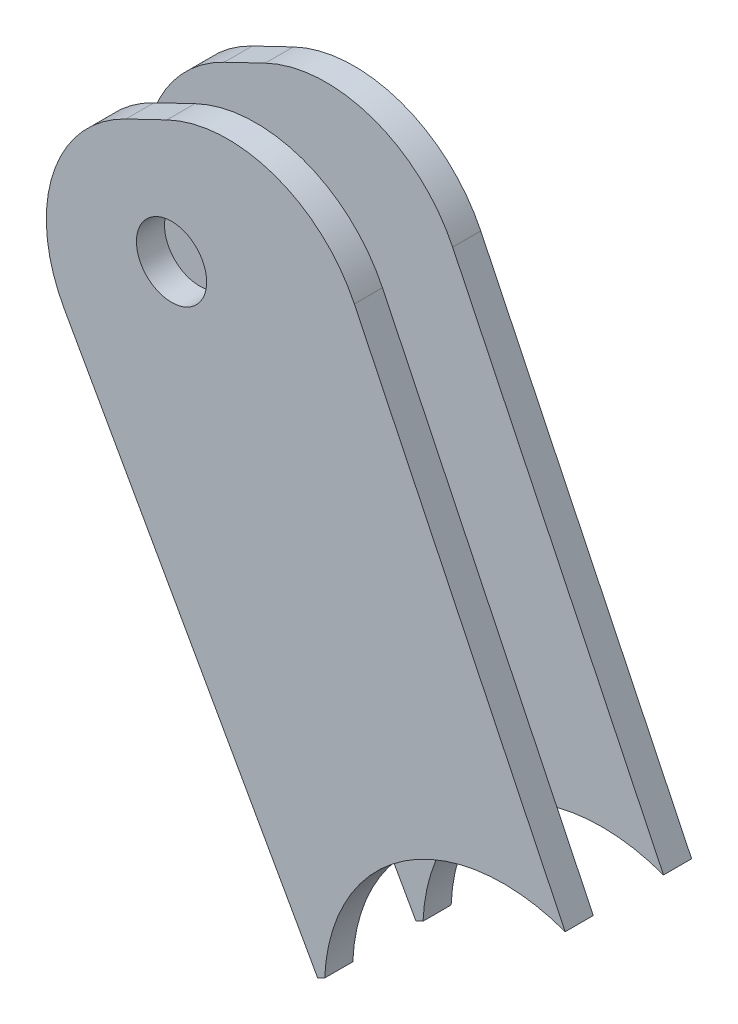
SolidWorks part; units mm, degrees
material "1.0037 (S235JR)"
ref_plane "Płaszczyzna XY" through (0, 0, 0) normal (0, 0, 1) x (1, 0, 0)
ref_plane "Płaszczyzna XZ" through (0, 0, 0) normal (0, 1, 0) x (1, 0, 0)
ref_plane "Płaszczyzna YZ" through (0, 0, 0) normal (1, 0, 0) x (0, 0, -1)
sketch "Szkic1" plane through (0, 0, 0) normal (0, 0, 1) x (1, 0, 0)
  line L0 (207.5316, 219.2375) -> (210.4517, 220.6423)
  line L5 (223.7984, 215.9663) -> (240.051, 182.1835)
  line L6 (240.051, 182.1835) -> (221.1833, 173.1064)
  line L7 (221.1833, 173.1064) -> (203.1408, 205.342)
  circle A2 centre (210.7813, 212.0576) radius 2.5 construction
  circle A3 centre (210.7813, 212.0576) radius 2.5
  arc A4 (210.4517, 220.6423) -> (223.7984, 215.9663) centre (214.787, 211.631) cw
  arc A5 (207.5316, 219.2375) -> (203.1408, 205.342) centre (211.867, 210.2261) ccw
  point P11 (219.508, 177.5147)
  point P12 (216.9531, 176.5117)
  point P13 (0, 0)
  point P14 (239.0727, 184.2171)
  point P15 (221.1833, 173.1064)
  dimension "D1" = 10
extrude "Dodanie-wyciągnięcie1" add sketch "Szkic1" along normal blind 2
sketch "Szkic2" plane through (0, 0, -5) normal (0, 0, -1) x (-1, 0, 0)
  line L4 (-240.051, 182.1835) -> (-221.1833, 173.1064)
  line L5 (-240.051, 182.1835) -> (-221.1833, 173.1064)
  line L6 (-223.7984, 215.9663) -> (-240.051, 182.1835)
  line L7 (-207.5316, 219.2375) -> (-210.4517, 220.6423)
  line L10 (-223.7984, 215.9663) -> (-240.051, 182.1835)
  line L11 (-207.5316, 219.2375) -> (-210.4517, 220.6423)
  line L12 (-221.1833, 173.1064) -> (-203.1408, 205.342)
  line L13 (-221.1833, 173.1064) -> (-203.1408, 205.342)
  circle A0 centre (-210.7813, 212.0576) radius 2.5 construction
  circle A1 centre (-210.7813, 212.0576) radius 2.5
  arc A2 (-210.4517, 220.6423) -> (-223.7984, 215.9663) centre (-214.787, 211.631) ccw
  arc A3 (-203.1408, 205.342) -> (-207.5316, 219.2375) centre (-211.867, 210.2261) ccw
  arc A4 (-210.4517, 220.6423) -> (-223.7984, 215.9663) centre (-214.787, 211.631) ccw
  arc A5 (-203.1408, 205.342) -> (-207.5316, 219.2375) centre (-211.867, 210.2261) ccw
  dimension "D1" = 0
extrude "Dodanie-wyciągnięcie2" add sketch "Szkic2" along normal blind 2 separate body
sketch "Szkic3" plane through (0, 0, 2) normal (0, 0, 1) x (1, 0, 0)
  circle A0 centre (234.4212, 172.7953) radius 12.7458
extrude "Wytnij-wyciągnięcie1" cut sketch "Szkic3" against normal blind 12
